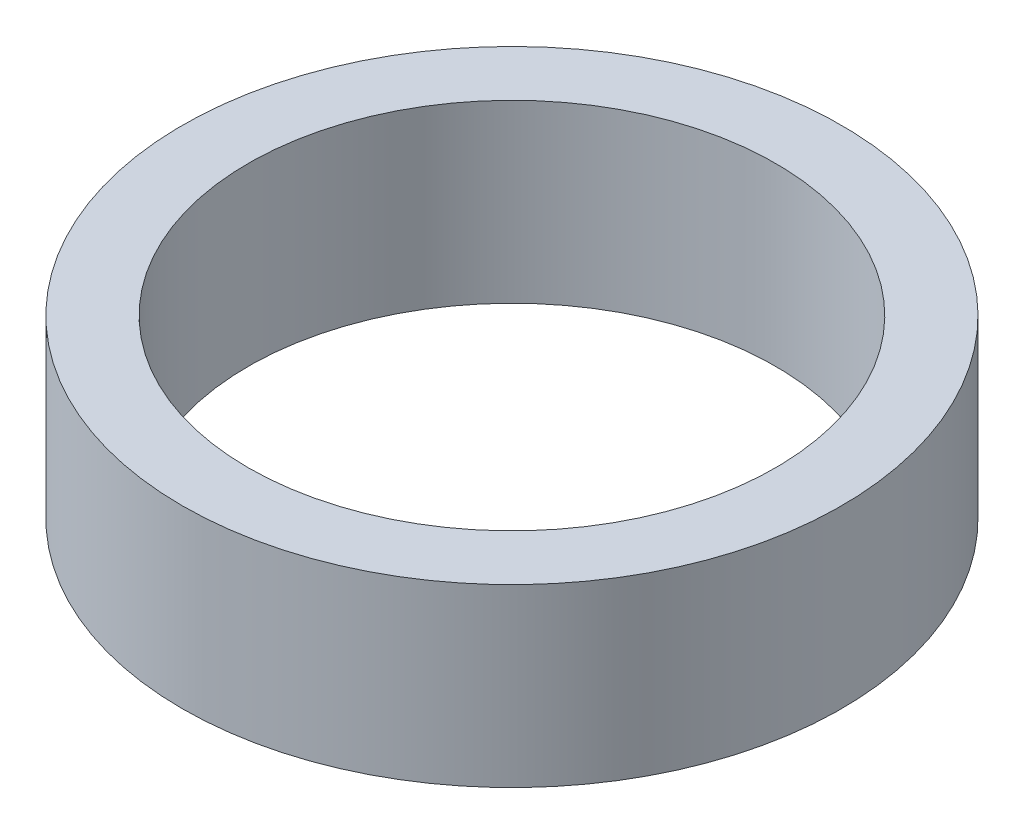
SolidWorks part; units mm, degrees
material "Markforged"
ref_plane "Front Plane" through (0, 0, 0) normal (0, 0, 1) x (1, 0, 0)
ref_plane "Top Plane" through (0, 0, 0) normal (0, 1, 0) x (1, 0, 0)
ref_plane "Right Plane" through (0, 0, 0) normal (1, 0, 0) x (0, 0, -1)
other "Bounding Box"
ref_plane "Default Plane" through (-8.9266, -12.7485, 0) normal (-0.1736, 0.9848, 0) x (0.9848, 0.1736, 0)
sketch "Sketch1" plane through (0, 0, 0) normal (0, 1, 0) x (1, 0, 0)
  circle A0 centre (0, 0) radius 18
  circle A1 centre (0, 0) radius 22.5
  dimension "D1" = 36
  dimension "D2" = 45
extrude "Boss-Extrude1" add sketch "Sketch1" along normal blind 12
